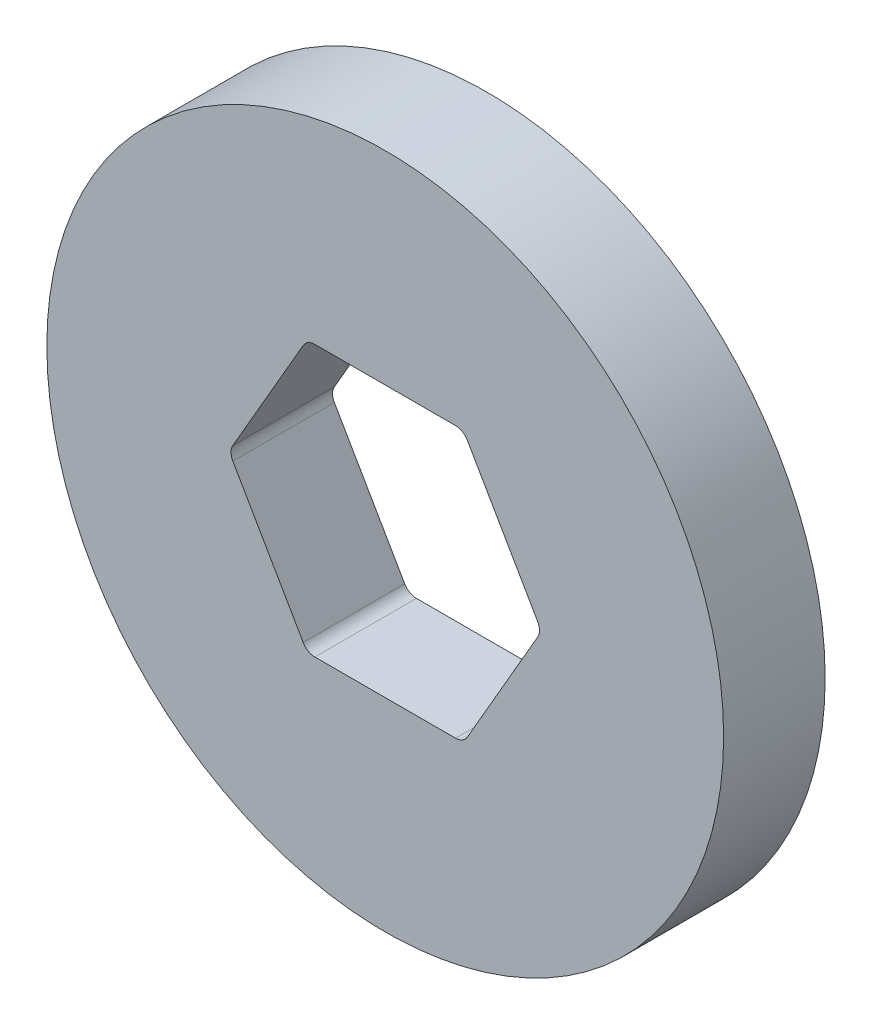
SolidWorks part; units mm, degrees
material "Tungsten"
ref_plane "Front Plane" through (0, 0, 0) normal (0, 0, 1) x (1, 0, 0)
ref_plane "Top Plane" through (0, 0, 0) normal (0, 1, 0) x (1, 0, 0)
ref_plane "Right Plane" through (0, 0, 0) normal (1, 0, 0) x (0, 0, -1)
sketch "Sketch1" plane through (0, 0, 0) normal (0, 0, 1) x (1, 0, 0)
  line L1 (23.094, 0) -> (11.547, 20)
  line L2 (11.547, 20) -> (-11.547, 20)
  line L3 (-11.547, 20) -> (-23.094, 0)
  line L4 (-23.094, 0) -> (-11.547, -20)
  line L5 (-11.547, -20) -> (11.547, -20)
  line L6 (11.547, -20) -> (23.094, 0)
  circle A0 centre (0, 0) radius 20 construction
  circle A1 centre (0, 0) radius 50
  point P10 (0, 20)
  dimension "D1" = 100
  dimension "D2" = 40
extrude "Boss-Extrude1" add sketch "Sketch1" along normal mid plane 15
fillet "Fillet1" radius 2 6 edges at (11.547, 20, 0) (-11.547, 20, 0) (-23.094, 0, 0) (11.547, -20, 0) (23.094, 0, 0) (-11.547, -20, 0)
